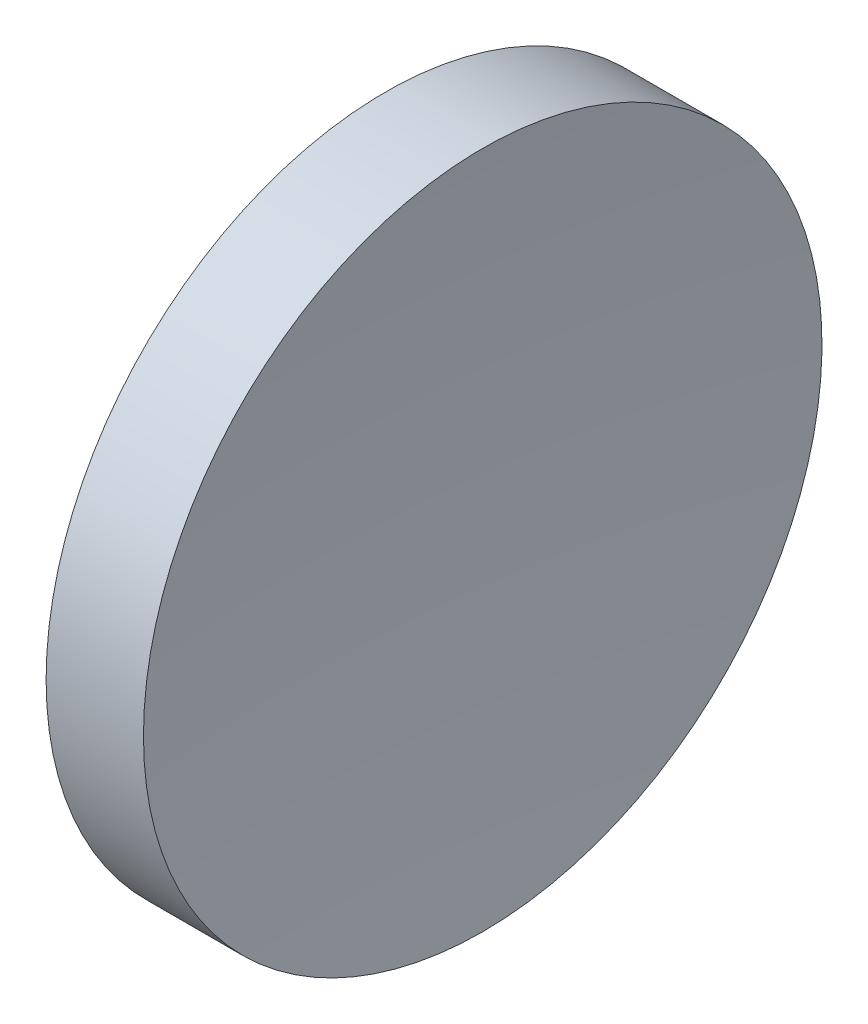
SolidWorks part; units mm, degrees
ref_plane "前视基准面" through (0, 0, 0) normal (0, 0, 1) x (1, 0, 0)
ref_plane "上视基准面" through (0, 0, 0) normal (0, 1, 0) x (1, 0, 0)
ref_plane "右视基准面" through (0, 0, 0) normal (1, 0, 0) x (0, 0, -1)
sketch "草图1" plane through (0, 0, 0) normal (0, 0, 1) x (1, 0, 0)
  line L0 (217.9703, 138.756) -> (265.5527, 138.756) construction
  line L1 (230.1996, 138.756) -> (230.1996, 176.256)
  line L2 (230.1996, 176.256) -> (240.9613, 176.256)
  line L3 (239.1996, 138.756) -> (230.1996, 138.756)
  arc A0 (240.9613, 176.256) -> (239.1996, 138.756) centre (639.1996, 138.756) ccw
  dimension "D1" = 400
revolve "旋转1" add sketch "草图1" angle 360 about L0
